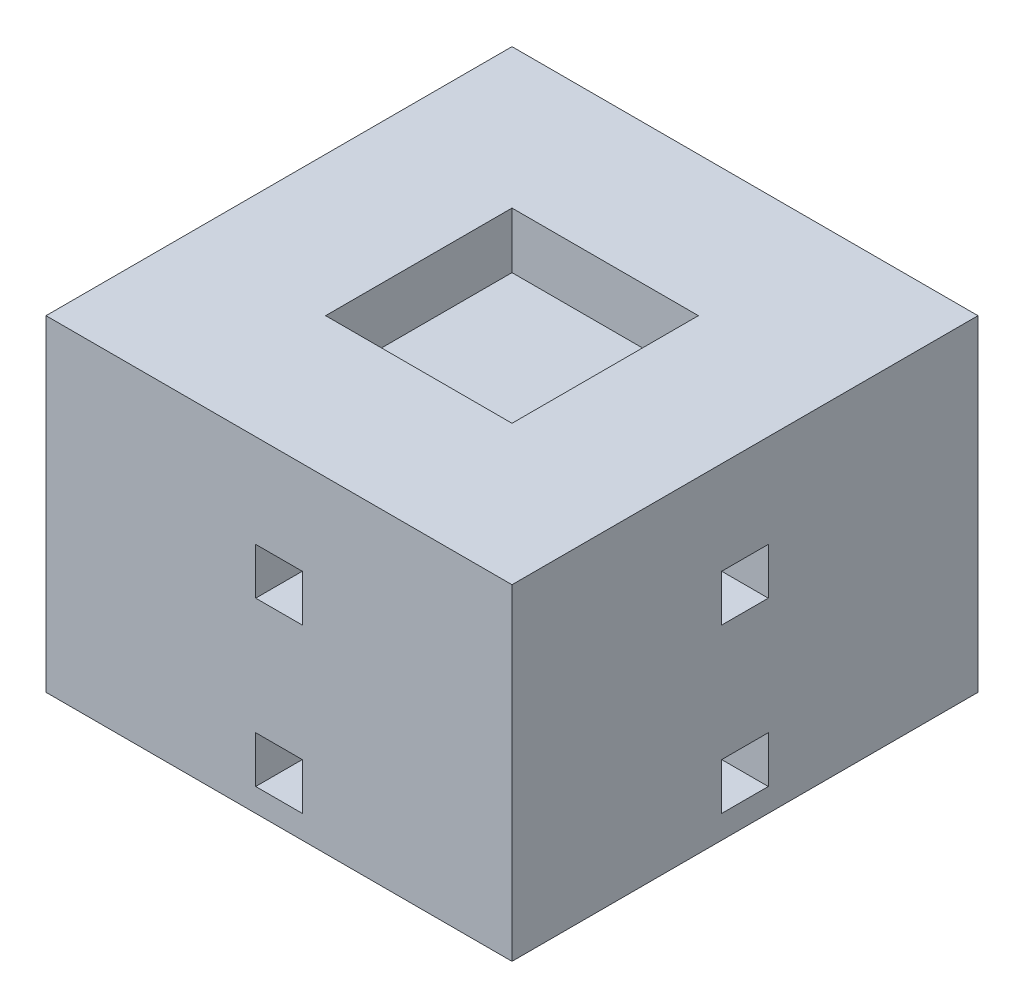
SolidWorks part; units mm, degrees
ref_plane "Front Plane" through (0, 0, 0) normal (0, 0, 1) x (1, 0, 0)
ref_plane "Top Plane" through (0, 0, 0) normal (0, 1, 0) x (1, 0, 0)
ref_plane "Right Plane" through (0, 0, 0) normal (1, 0, 0) x (0, 0, -1)
sketch "Sketch1" plane through (0, 0, 0) normal (0, 1, 0) x (1, 0, 0)
  line L1 (-25, -25) -> (25, -25)
  line L2 (-25, -25) -> (-25, 25)
  line L3 (-25, 25) -> (25, 25)
  line L4 (25, -25) -> (25, 25)
  line L5 (-25, -25) -> (25, 25) construction
  line L6 (-25, 25) -> (25, -25) construction
  point P0 (0, 0)
extrude "Boss-Extrude1" add sketch "Sketch1" along normal blind 35
sketch "Sketch3" plane through (-25, 0, 0) normal (-1, 0, 0) x (0, 0, 1)
  line L0 (-2.5, 2.5) -> (2.5, 2.5)
  line L1 (-2.5, 2.5) -> (-2.5, 7.5)
  line L2 (-2.5, 7.5) -> (2.5, 7.5)
  line L3 (-2.5, 20) -> (2.5, 20)
  line L4 (-2.5, 20) -> (-2.5, 25)
  line L5 (-2.5, 25) -> (2.5, 25)
  line L6 (2.5, 20) -> (2.5, 25)
  line L7 (-2.5, 20) -> (2.5, 25) construction
  line L8 (-2.5, 25) -> (2.5, 20) construction
  line L9 (2.5, 2.5) -> (2.5, 7.5)
  line L10 (-2.5, 2.5) -> (2.5, 7.5) construction
  line L11 (-2.5, 7.5) -> (2.5, 2.5) construction
  line L12 (25, 35) -> (25, 0) construction
  line L14 (-25, 0) -> (25, 0) construction
  line L15 (-25, 35) -> (25, 35) construction
  line L16 (-25, 10) -> (25, 10) construction
  line L17 (-25, 35) -> (-25, 0) construction
  line L18 (-25, 35) -> (25, 0) construction
  line L19 (-25, 0) -> (25, 35) construction
  point P0 (0, 5)
  point P7 (0, 35)
  point P8 (0, 22.5)
  dimension "D1" = 22.5
  dimension "D2" = 2.5
  dimension "D3" = 5
  dimension "D4" = 5
  dimension "D5" = 22.5
  dimension "D6" = 5
  dimension "D7" = 5
  dimension "D8" = 10
  dimension "D9" = 10
  dimension "D10" = 12.5
extrude "Cut-Extrude2" cut sketch "Sketch3" against normal blind 6
sketch "Sketch4" plane through (0, 0, -25) normal (0, 0, -1) x (-1, 0, 0)
  line L0 (-2.5, 2.5) -> (2.5, 2.5)
  line L1 (-2.5, 2.5) -> (-2.5, 7.5)
  line L2 (-2.5, 7.5) -> (2.5, 7.5)
  line L3 (-2.5, 20) -> (2.5, 20)
  line L4 (-2.5, 20) -> (-2.5, 25)
  line L5 (-2.5, 25) -> (2.5, 25)
  line L6 (2.5, 20) -> (2.5, 25)
  line L7 (-2.5, 20) -> (2.5, 25) construction
  line L8 (-2.5, 25) -> (2.5, 20) construction
  line L9 (2.5, 2.5) -> (2.5, 7.5)
  line L10 (-2.5, 2.5) -> (2.5, 7.5) construction
  line L11 (-2.5, 7.5) -> (2.5, 2.5) construction
  line L12 (-25, 10) -> (25, 10) construction
  line L15 (25, 35) -> (25, 0) construction
  line L16 (-25, 0) -> (25, 0) construction
  line L17 (-25, 35) -> (25, 35) construction
  line L18 (-25, 35) -> (-25, 0) construction
  point P0 (0, 5)
  point P9 (0, 22.5)
  dimension "D1" = 5
  dimension "D2" = 5
  dimension "D3" = 5
  dimension "D4" = 5
  dimension "D5" = 12.5
  dimension "D6" = 22.5
  dimension "D7" = 22.5
  dimension "D8" = 10
  dimension "D9" = 10
  dimension "D10" = 2.5
extrude "Cut-Extrude3" cut sketch "Sketch4" against normal blind 5
sketch "Sketch5" plane through (25, 0, 0) normal (1, 0, 0) x (0, 0, -1)
  line L0 (-25, 35) -> (25, 0) construction
  line L1 (-2.5, 2.5) -> (2.5, 2.5)
  line L2 (-25, 0) -> (25, 35) construction
  line L3 (25, 35) -> (25, 0) construction
  line L4 (-25, 0) -> (25, 0) construction
  line L5 (-25, 35) -> (25, 35) construction
  line L9 (-2.5, 2.5) -> (-2.5, 7.5)
  line L10 (-2.5, 7.5) -> (2.5, 7.5)
  line L11 (-2.5, 20) -> (2.5, 20)
  line L12 (-2.5, 20) -> (-2.5, 25)
  line L13 (-2.5, 25) -> (2.5, 25)
  line L14 (2.5, 20) -> (2.5, 25)
  line L15 (-2.5, 20) -> (2.5, 25) construction
  line L16 (-2.5, 25) -> (2.5, 20) construction
  line L17 (2.5, 2.5) -> (2.5, 7.5)
  line L18 (-2.5, 2.5) -> (2.5, 7.5) construction
  line L19 (-2.5, 7.5) -> (2.5, 2.5) construction
  line L20 (-25.0503, 10.0251) -> (24.9497, 10.0251) construction
  line L21 (-25.0503, 35.0251) -> (24.9497, 0.0251) construction
  line L22 (-25.0503, 0.0251) -> (24.9497, 35.0251) construction
  point P4 (0, 17.5)
  point P5 (0, 5)
  point P18 (0, 22.5)
  dimension "D1" = 5
  dimension "D2" = 5
  dimension "D3" = 5
  dimension "D4" = 5
  dimension "D5" = 12.5
  dimension "D6" = 22.5
  dimension "D7" = 22.5
  dimension "D8" = 2.5
  dimension "D9" = 10
extrude "Cut-Extrude4" cut sketch "Sketch5" against normal blind 6
sketch "Sketch6" plane through (0, 0, 25) normal (0, 0, 1) x (1, 0, 0)
  line L0 (-2.5, 2.5) -> (2.5, 2.5)
  line L1 (-2.5, 2.5) -> (-2.5, 7.5)
  line L2 (-2.5, 7.5) -> (2.5, 7.5)
  line L3 (-2.5, 20) -> (2.5, 20)
  line L4 (-2.5, 20) -> (-2.5, 25)
  line L5 (-2.5, 25) -> (2.5, 25)
  line L6 (2.5, 20) -> (2.5, 25)
  line L7 (-2.5, 20) -> (2.5, 25) construction
  line L8 (-2.5, 25) -> (2.5, 20) construction
  line L9 (2.5, 2.5) -> (2.5, 7.5)
  line L10 (-2.5, 2.5) -> (2.5, 7.5) construction
  line L11 (-2.5, 7.5) -> (2.5, 2.5) construction
  line L12 (-25.0503, 10) -> (24.9497, 10) construction
  line L13 (-25.0503, 35.1046) -> (24.9497, 0.1046) construction
  line L14 (-25.0503, 0.1046) -> (24.9497, 35.1046) construction
  line L15 (25, 35) -> (25, 0) construction
  line L16 (-25, 0) -> (25, 0) construction
  line L17 (-25, 35) -> (25, 35) construction
  point P0 (0, 5)
  point P9 (0, 22.5)
  dimension "D1" = 5
  dimension "D2" = 5
  dimension "D3" = 5
  dimension "D4" = 5
  dimension "D5" = 12.5
  dimension "D6" = 22.5
  dimension "D7" = 22.5
  dimension "D8" = 2.5
  dimension "D9" = 10
  dimension "D10" = 10
extrude "Cut-Extrude5" cut sketch "Sketch6" against normal blind 6
sketch "Sketch7" plane through (0, 0, 0) normal (0, -1, 0) x (-1, 0, 0)
  line L1 (10, 10) -> (-10, 10)
  line L2 (10, 10) -> (10, -10)
  line L3 (10, -10) -> (-10, -10)
  line L4 (-10, 10) -> (-10, -10)
  line L5 (10, 10) -> (-10, -10) construction
  line L6 (10, -10) -> (-10, 10) construction
  point P0 (0, 0)
extrude "Cut-Extrude6" cut sketch "Sketch7" against normal blind 6
sketch "Sketch8" plane through (0, 35, 0) normal (0, 1, 0) x (1, 0, 0)
  line L1 (10, -10) -> (-10, -10)
  line L2 (10, -10) -> (10, 10)
  line L3 (10, 10) -> (-10, 10)
  line L4 (-10, -10) -> (-10, 10)
  line L5 (10, -10) -> (-10, 10) construction
  line L6 (10, 10) -> (-10, -10) construction
  point P0 (0, 0)
extrude "Cut-Extrude7" cut sketch "Sketch8" against normal blind 6
